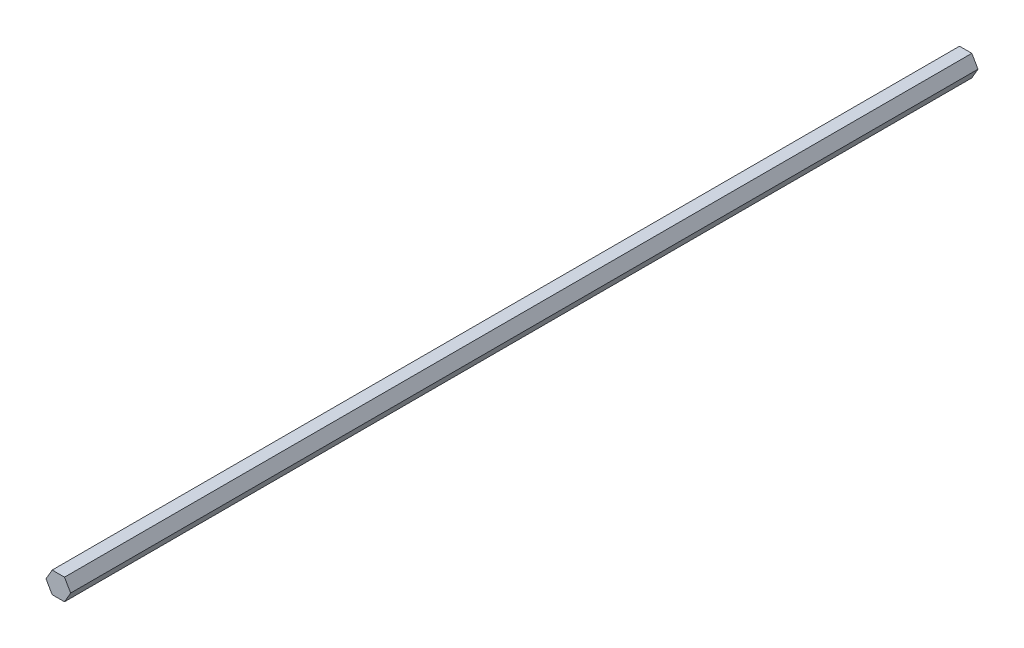
SolidWorks part; units mm, degrees
ref_plane "Front Plane" through (0, 0, 0) normal (0, 0, 1) x (1, 0, 0)
ref_plane "Top Plane" through (0, 0, 0) normal (0, 1, 0) x (1, 0, 0)
ref_plane "Right Plane" through (0, 0, 0) normal (1, 0, 0) x (0, 0, -1)
sketch "Sketch1" plane through (0, 0, 0) normal (0, 0, 1) x (1, 0, 0)
  line L1 (7.3323, 0) -> (3.6662, 6.35)
  line L2 (3.6662, 6.35) -> (-3.6662, 6.35)
  line L3 (-3.6662, 6.35) -> (-7.3323, 0)
  line L4 (-7.3323, 0) -> (-3.6662, -6.35)
  line L5 (-3.6662, -6.35) -> (3.6662, -6.35)
  line L6 (3.6662, -6.35) -> (7.3323, 0)
  circle A0 centre (0, 0) radius 6.35 construction
  dimension "D1" = 12.7
extrude "Boss-Extrude1" add sketch "Sketch1" along normal blind 539.75
